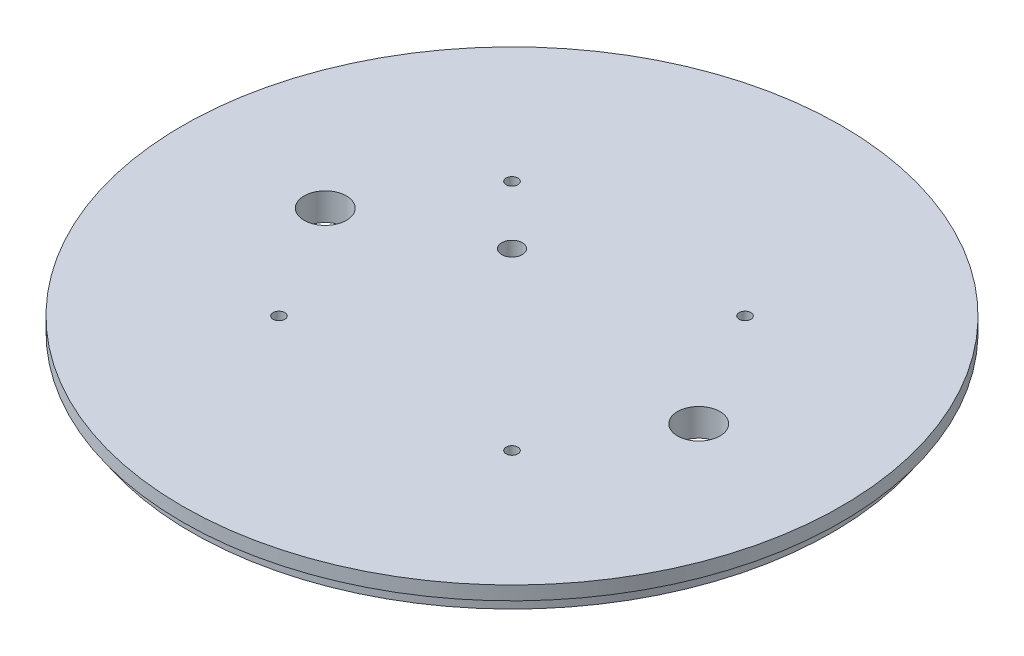
SolidWorks part; units mm, degrees
material "6061-T6 (SS)"
ref_plane "Front Plane" through (0, 0, 0) normal (0, 0, 1) x (1, 0, 0)
ref_plane "Top Plane" through (0, 0, 0) normal (0, 1, 0) x (1, 0, 0)
ref_plane "Right Plane" through (0, 0, 0) normal (1, 0, 0) x (0, 0, -1)
sketch "Sketch1" plane through (0, 0, 0) normal (0, 1, 0) x (1, 0, 0)
  line L0 (0, -76.2) -> (0, 76.2) construction
  line L1 (-76.2, 0) -> (76.2, 0) construction
  line L2 (-26.9408, 26.9408) -> (0, 0) construction
  line L3 (0, 56.7387) -> (0, 29.6936) construction
  line L4 (3.6407, 56.7387) -> (3.6407, 29.6936) construction
  line L5 (-3.6407, 56.7387) -> (-3.6407, 29.6936) construction
  line L6 (0, -56.7387) -> (0, -29.6936) construction
  line L7 (3.6407, -56.7387) -> (3.6407, -29.6936) construction
  line L8 (-3.6407, -56.7387) -> (-3.6407, -29.6936) construction
  line L9 (-53.8815, -53.8815) -> (54.3236, 54.3236) construction
  circle A0 centre (0, 0) radius 76.2
  circle A1 centre (0, 0) radius 3.175 construction
  circle A2 centre (43.18, 0) radius 4.9022
  circle A3 centre (-43.18, 0) radius 4.9022
  circle A4 centre (-26.9408, 26.9408) radius 1.3589
  arc A6 (3.6407, 56.7387) -> (-3.6407, 56.7387) centre (0, 56.7387) ccw construction
  arc A7 (-3.6407, 29.6936) -> (3.6407, 29.6936) centre (0, 29.6936) ccw construction
  arc A8 (3.6407, -56.7387) -> (-3.6407, -56.7387) centre (0, -56.7387) cw construction
  arc A9 (-3.6407, -29.6936) -> (3.6407, -29.6936) centre (0, -29.6936) cw construction
  circle A10 centre (26.9408, -26.9408) radius 1.3589
  circle A11 centre (-13.4704, 13.4704) radius 2.3813
  circle A12 centre (-26.9408, -26.9408) radius 1.3589
  circle A13 centre (26.9408, 26.9408) radius 1.3589
  circle A14 centre (-26.9408, 26.9408) radius 1.3589
  circle A15 centre (26.9408, -26.9408) radius 1.3589
  circle A16 centre (26.9408, 26.9408) radius 1.3589
  circle A17 centre (-26.9408, -26.9408) radius 1.3589
  point P16 (0, 43.2162)
  point P19 (0, 0)
  point P26 (0, -43.2162)
  point P50 (0, 0)
  dimension "D1" = 152.4
  dimension "D2" = 6.35
  dimension "D3" = 9.8044
  dimension "D5" = 2.7178
  dimension "D8" = 4.7625
  dimension "D6" = 38.1
  dimension "D7" = 45
  dimension "D4" = 45
  dimension "D9" = 43.18
  dimension "D10" = 4
extrude "Boss-Extrude1" add sketch "Sketch1" along normal blind 6.35 contours A0 A13 A10 A4 A2 A3 A11 A12
sketch "Sketch2" plane through (0, 0, 0) normal (0, -1, 0) x (1, 0, 0)
  circle A0 centre (0, 0) radius 76.2
  circle A1 centre (0, 0) radius 74.041
  dimension "D1" = 152.4
  dimension "D2" = 148.082
extrude "Cut-Extrude1" cut sketch "Sketch2" against normal blind 3.175
sketch "Sketch3" plane through (0, 6.35, 0) normal (0, 1, 0) x (1, 0, 0)
  line L0 (0, 76.2) -> (0, -76.2) construction
  line L1 (-76.2, 0) -> (76.2, 0) construction
  line L2 (0, 34.798) -> (0, 13.97) construction
  line L3 (3.2385, 34.798) -> (3.2385, 13.97)
  line L4 (-3.2385, 34.798) -> (-3.2385, 13.97)
  line L5 (0, -34.798) -> (0, -13.97) construction
  line L6 (3.2385, -34.798) -> (3.2385, -13.97)
  line L7 (-3.2385, -34.798) -> (-3.2385, -13.97)
  arc A1 (3.2385, 34.798) -> (-3.2385, 34.798) centre (0, 34.798) ccw
  arc A2 (-3.2385, 13.97) -> (3.2385, 13.97) centre (0, 13.97) ccw
  arc A3 (3.2385, -34.798) -> (-3.2385, -34.798) centre (0, -34.798) cw
  arc A4 (-3.2385, -13.97) -> (3.2385, -13.97) centre (0, -13.97) cw
  point P7 (0, 13.97)
  point P8 (0, 34.798)
  point P12 (0, 24.384)
  point P20 (0, -24.384)
  point P25 (0, -34.798)
  point P26 (0, -13.97)
  dimension "D1" = 13.97
  dimension "D2" = 20.828
  dimension "D3" = 6.477
extrude "Cut-Extrude2" cut sketch "Sketch3" against normal blind 3.556 from offset 3.175
equation "\"leadDist\"=1.5"
equation "\"Lead_Screw_Dist\" = 3.4in"
equation "\"Lead_Screw_Diam\" = 0.386in"
equation "\"D3@Sketch1\"=\"Lead_Screw_Diam\""
equation "\"D9@Sketch1\"=\"Lead_Screw_Dist\"/2"
